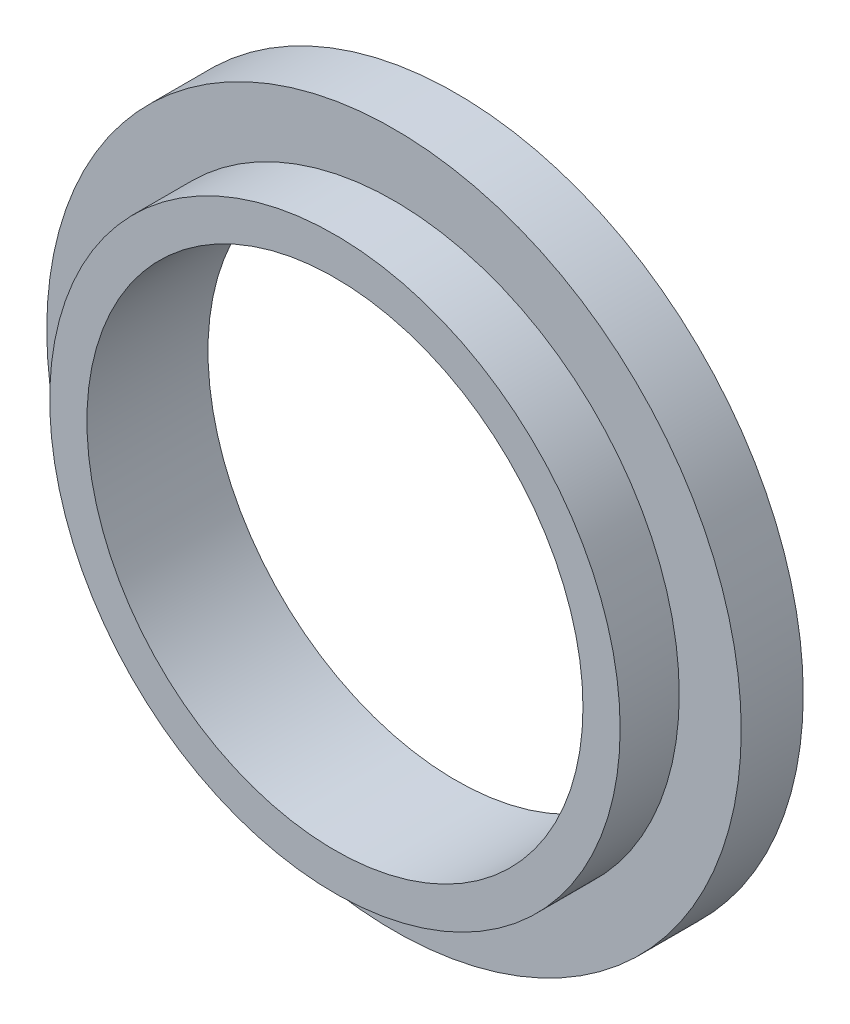
SolidWorks part; units mm, degrees
ref_plane "Front" through (0, 0, 0) normal (0, 0, 1) x (1, 0, 0)
ref_plane "Top" through (0, 0, 0) normal (0, 1, 0) x (1, 0, 0)
ref_plane "Right" through (0, 0, 0) normal (1, 0, 0) x (0, 0, -1)
sketch "Sketch1" plane through (0, 0, 0) normal (0, 0, 1) x (1, 0, 0)
  circle A0 centre (0, 0) radius 28
  dimension "D1" = 56
extrude "Boss-Extrude1" add sketch "Sketch1" along normal blind 5
sketch "Sketch2" plane through (0, 0, 5) normal (0, 0, 1) x (1, 0, 0)
  circle A0 centre (0, 0) radius 23
  dimension "D1" = 46
extrude "Boss-Extrude2" add sketch "Sketch2" along normal blind 4.7625
sketch "Sketch3" plane through (0, 0, 9.7625) normal (0, 0, 1) x (1, 0, 0)
  circle A0 centre (0, 0) radius 20
  dimension "D1" = 40
extrude "Cut-Extrude1" cut sketch "Sketch3" against normal through all both and the other way through all
